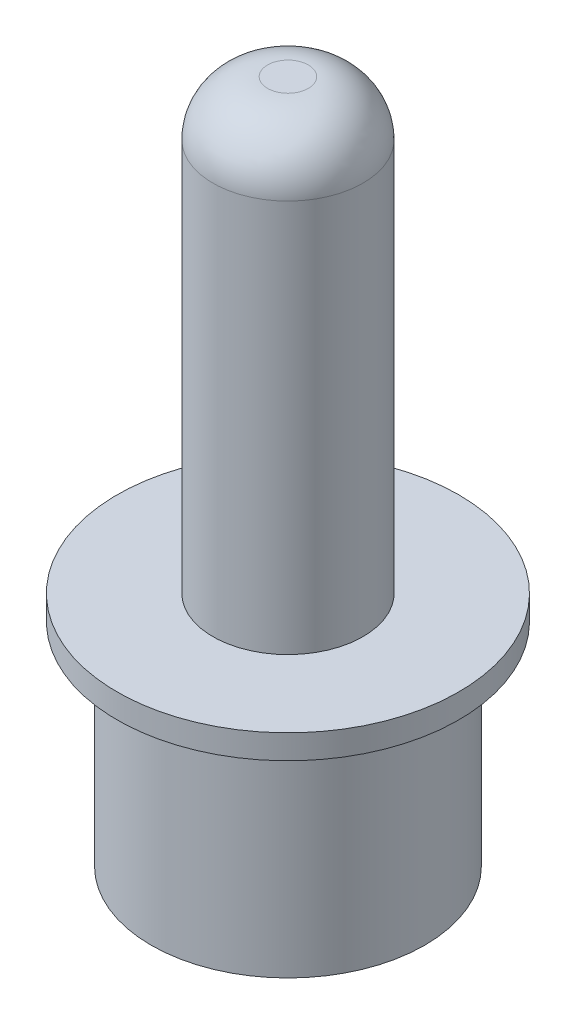
SolidWorks part; units mm, degrees
material "1060 Alloy"
ref_plane "Front Plane" through (0, 0, 0) normal (0, 0, 1) x (1, 0, 0)
ref_plane "Top Plane" through (0, 0, 0) normal (0, 1, 0) x (1, 0, 0)
ref_plane "Right Plane" through (0, 0, 0) normal (1, 0, 0) x (0, 0, -1)
sketch "Sketch1" plane through (0, 0, 0) normal (0, 0, 1) x (1, 0, 0)
  line L0 (0, 0) -> (0, 25)
  line L1 (0, 0) -> (-5, 0)
  line L2 (-5, 0) -> (-5, 7.3431)
  line L3 (-5, 7.3431) -> (-6.2441, 7.7559)
  line L4 (-6.2441, 7.7559) -> (-6.2441, 8.6421)
  line L5 (-6.2441, 8.6421) -> (-2.7441, 8.6421)
  line L6 (-2.7441, 8.6421) -> (-2.7441, 25)
  line L7 (-2.7441, 25) -> (0, 25)
revolve "Revolve1" add sketch "Sketch1" angle 360 about L0
fillet "Fillet1" radius 2 1 edges at (0, 25, -2.7441)
sketch "Sketch2" plane through (0, 0, 0) normal (0, -1, 0) x (1, 0, 0)
  circle A0 centre (0, 0) radius 1.5
extrude "Cut-Extrude1" cut sketch "Sketch2" against normal blind 18
